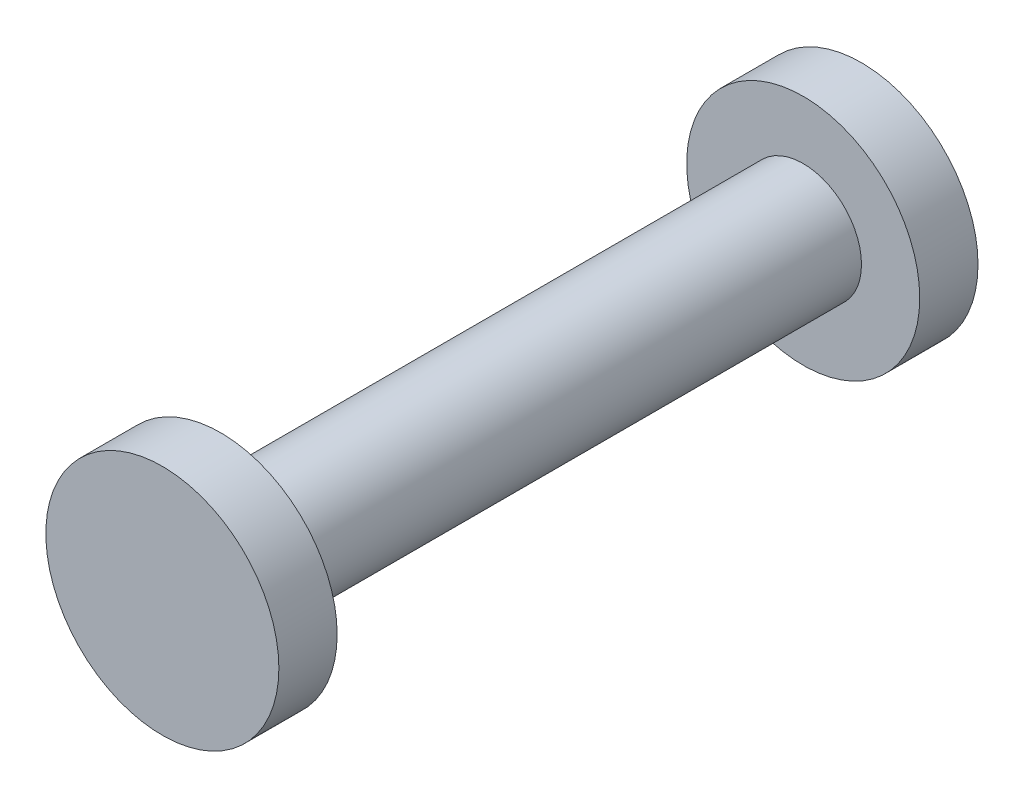
SolidWorks part; units mm, degrees
ref_plane "Front Plane" through (0, 0, 0) normal (0, 0, 1) x (1, 0, 0)
ref_plane "Top Plane" through (0, 0, 0) normal (0, 1, 0) x (1, 0, 0)
ref_plane "Right Plane" through (0, 0, 0) normal (1, 0, 0) x (0, 0, -1)
sketch "Sketch1" plane through (0, 0, 0) normal (0, 0, 1) x (1, 0, 0)
  circle A0 centre (0, 0) radius 5
  dimension "D1" = 10
extrude "Boss-Extrude1" add sketch "Sketch1" along normal mid plane 50 contours A0
sketch "Sketch2" plane through (0, 0, 25) normal (0, 0, 1) x (1, 0, 0)
  circle A0 centre (0, 0) radius 10
  dimension "D1" = 20
extrude "Boss-Extrude2" add sketch "Sketch2" along normal blind 5 contours A0
mirror "Mirror1" about plane through (0, 0, 0) normal (0, 0, 1) of "Boss-Extrude2"
